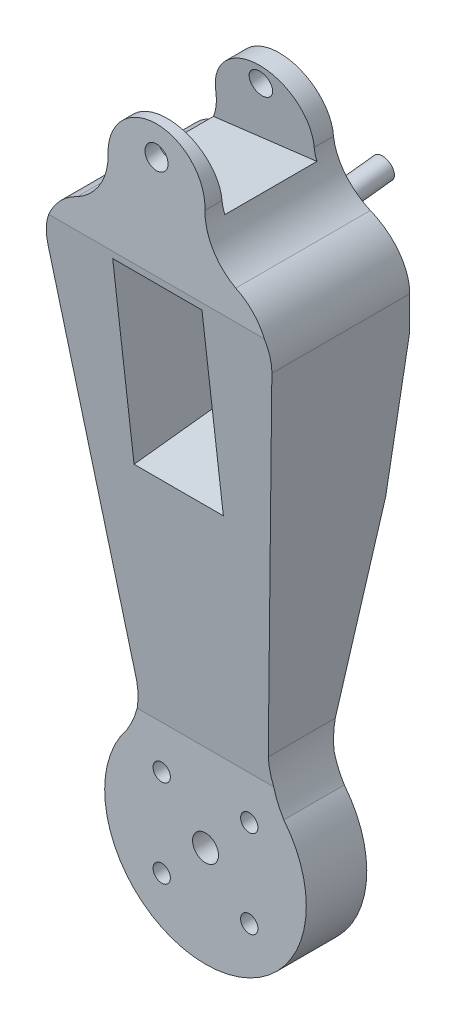
SolidWorks part; units mm, degrees
ref_plane "Front Plane" through (0, 0, 0) normal (0, 0, 1) x (1, 0, 0)
ref_plane "Top Plane" through (0, 0, 0) normal (0, 1, 0) x (1, 0, 0)
ref_plane "Right Plane" through (0, 0, 0) normal (1, 0, 0) x (0, 0, -1)
sketch "Sketch1" plane through (0, 0, 0) normal (0, 0, 1) x (1, 0, 0)
  line L0 (0, 200) -> (0, 0) construction
  line L1 (-22.8275, 39.2926) -> (-38.8801, 170.03)
  line L2 (22.8275, 39.2926) -> (38.8801, 170.03)
  arc A0 (-27.2151, 22.0077) -> (27.2151, 22.0077) centre (0, 0) ccw
  arc A2 (-38.8801, 170.03) -> (-27.5332, 190.5693) centre (-19.0291, 172.4673) cw
  arc A4 (38.8801, 170.03) -> (27.5332, 190.5693) centre (19.0291, 172.4673) ccw
  arc A10 (16.7909, 208.5331) -> (-16.7909, 208.5331) centre (0, 209.3997) ccw
  arc A11 (-27.5332, 190.5693) -> (-16.7909, 208.5331) centre (-37.034, 208.4446) ccw
  arc A12 (27.5332, 190.5693) -> (16.7909, 208.5331) centre (37.034, 208.4446) cw
  arc A13 (-22.8275, 39.2926) -> (-27.2151, 22.0077) centre (-51.9369, 37.4823) cw
  arc A14 (22.8275, 39.2926) -> (27.2151, 22.0077) centre (51.9369, 37.4823) ccw
  dimension "D1" = 70
  dimension "D2" = 209.3997
  dimension "D5" = 20
  dimension "D3" = 16.8132
  dimension "D6" = 7
extrude "Boss-Extrude1" add sketch "Sketch1" along normal blind 55
sketch "Sketch5" plane through (0, 0, 0) normal (0, 0, 1) x (1, 0, 0)
  line L1 (16.97, -20.5) -> (-16.97, -20.5)
  line L2 (20.5, -16.97) -> (20.5, 16.97)
  line L3 (16.97, 20.5) -> (-16.97, 20.5)
  line L4 (-20.5, -16.97) -> (-20.5, 16.97)
  line L5 (18.735, -18.735) -> (-20.5, 20.5) construction
  line L6 (20.5, 20.5) -> (-20.5, -20.5) construction
  line L7 (-16.97, 20.5) -> (-20.5, 16.97)
  line L10 (16.97, 20.5) -> (20.5, 16.97)
  line L13 (-20.5, -16.97) -> (-16.97, -20.5)
  line L16 (20.5, -16.97) -> (16.97, -20.5)
  point P0 (0, 0)
  dimension "D1" = 41
  dimension "D3" = 3.53
  dimension "D4" = 3.53
  dimension "D5" = 3.53
  dimension "D6" = 3.53
  dimension "D9" = 3.53
extrude "Cut-Extrude3" cut sketch "Sketch5" along normal blind 28
sketch "Sketch14" plane through (0, 0, 0) normal (0, 0, 1) x (1, 0, 0)
  circle A0 centre (0, 203.8964) radius 2
  dimension "D1" = 4
sketch "Sketch15" plane through (0, 0, 0) normal (1, 0, 0) x (0, 0, -1)
  line L0 (-38, -35) -> (-38, 30.1791)
  line L1 (-4.4013, 156.1236) -> (-12.4001, 226.7575)
  line L2 (-38, 30.1791) -> (-55, 180.2996)
  line L4 (-55, 180.2996) -> (-55, -35)
  line L5 (-38, -35) -> (-55, -35)
  line L6 (-17, -35) -> (-17, 30.6502)
  line L8 (0, 149.9148) -> (0, 117.2572)
  line L9 (-27.5, 226.2129) -> (-27.5, -35) construction
  line L10 (-4.4013, 156.1236) -> (-6.3495, 105.3692)
  line L11 (-17, -35) -> (0, -35)
  line L12 (0, 117.2572) -> (0, -35)
  line L13 (-17, 30.6502) -> (-6.3495, 105.3692)
  line L15 (-12.4001, 226.7575) -> (0, 226.2129)
  line L16 (0, 226.2129) -> (0, 149.9148)
extrude "Cut-Extrude4" cut sketch "Sketch15" against normal through all both and the other way through all
sketch "Sketch18" plane through (0, 0, 28) normal (0, 0, -1) x (-1, 0, 0)
  line L0 (-20.5, 16.97) -> (-20.5, -16.97) construction
  line L1 (-20.5, -16.97) -> (-16.97, -20.5) construction
  line L2 (-16.97, -20.5) -> (16.97, -20.5) construction
  line L3 (16.97, -20.5) -> (20.5, -16.97) construction
  line L4 (20.5, -16.97) -> (20.5, 16.97) construction
  line L5 (20.5, 16.97) -> (16.97, 20.5) construction
  line L6 (16.97, 20.5) -> (-16.97, 20.5) construction
  line L7 (-16.97, 20.5) -> (-20.5, 16.97) construction
  line L8 (-18.735, 18.735) -> (18.735, -18.735) construction
  line L9 (-18.735, -18.735) -> (18.735, 18.735) construction
  circle A0 centre (0, 0) radius 4.5
  circle A1 centre (-15.1995, 15.1995) radius 3
  circle A2 centre (15.1995, 15.1995) radius 3
  circle A3 centre (15.1995, -15.1995) radius 3
  circle A4 centre (-15.1995, -15.1995) radius 3
  point P33 (0, 0)
  dimension "D1" = 9
  dimension "D2" = 6
  dimension "D3" = 5
  dimension "D4" = 4
extrude "Cut-Extrude5" cut sketch "Sketch18" against normal through all both and the other way through all
sketch "Sketch20" plane through (-17.7356, -2.1777, 0) normal (-0.9925, -0.1219, 0) x (0, 0, 1)
  line L5 (16.5272, 200.6521) -> (48.5272, 200.6521)
  line L7 (16.5272, 200.6521) -> (19.5208, 224.6521)
  line L8 (55, 224.6521) -> (12.3242, 224.6521) construction
  line L9 (48.5272, 200.6521) -> (51.5208, 224.6521)
  line L10 (19.5208, 224.6521) -> (51.5208, 224.6521)
  dimension "D1" = 82.89
  dimension "D2" = 97.11
  dimension "D4" = 32
  dimension "D5" = 24
extrude "Cut-Extrude6" cut sketch "Sketch20" against normal through all both and the other way through all
sketch "Sketch21" plane through (0, -3.8666, 34.1446) normal (0, -0.1125, 0.9936) x (1, 0, 0)
  circle A0 centre (0, 220.965) radius 4
  ellipse E0 centre (0, 214.2586) end of major axis (16.8132, 214.2586) minor radius 16.7064 (16.7909, 213.3975) -> (-16.7909, 213.3975) ccw construction
  dimension "D1" = 8
  dimension "D2" = 10
extrude "Cut-Extrude7" cut sketch "Sketch21" against normal through all both and the other way through all
sketch "Sketch22" plane through (0, -3.8666, 34.1446) normal (0, -0.1125, 0.9936) x (1, 0, 0)
  line L0 (0, 213.2171) -> (0, 115.8465) construction
  line L1 (-15.5, 182.8503) -> (15.5, 182.8503)
  line L2 (-15.5, 182.8503) -> (-15.5, 116.8503)
  line L3 (-15.5, 116.8503) -> (15.5, 116.8503)
  line L4 (15.5, 182.8503) -> (15.5, 116.8503)
  dimension "D1" = 66
  dimension "D2" = 31
  dimension "D3" = 15.5
extrude "Cut-Extrude8" cut sketch "Sketch22" against normal blind 34
sketch "Sketch30" plane through (0, 1.4846, -13.1104) normal (0, 0.1125, -0.9936) x (-1, 0, 0)
  line L0 (37.1726, 155.6273) -> (-37.1726, 155.6273) construction
  circle A0 centre (0, 169.8573) radius 3.775
  dimension "D1" = 7.55
  dimension "D2" = 14.23
extrude "Boss-Extrude2" add sketch "Sketch30" along normal blind 30
sketch "Sketch31" plane through (0, 0, 0) normal (0, 0, 1) x (1, 0, 0)
  line L0 (-16.7124, 40.0924) -> (-23.5385, 98.9323)
  line L1 (-23.5385, 98.9323) -> (19.6832, 98.9323)
  line L2 (19.6832, 98.9323) -> (14.9082, 40.0924)
  line L3 (-16.7124, 40.0924) -> (14.9082, 40.0924)
extrude "Cut-Extrude9" cut sketch "Sketch31" along normal blind 15 from offset 20
